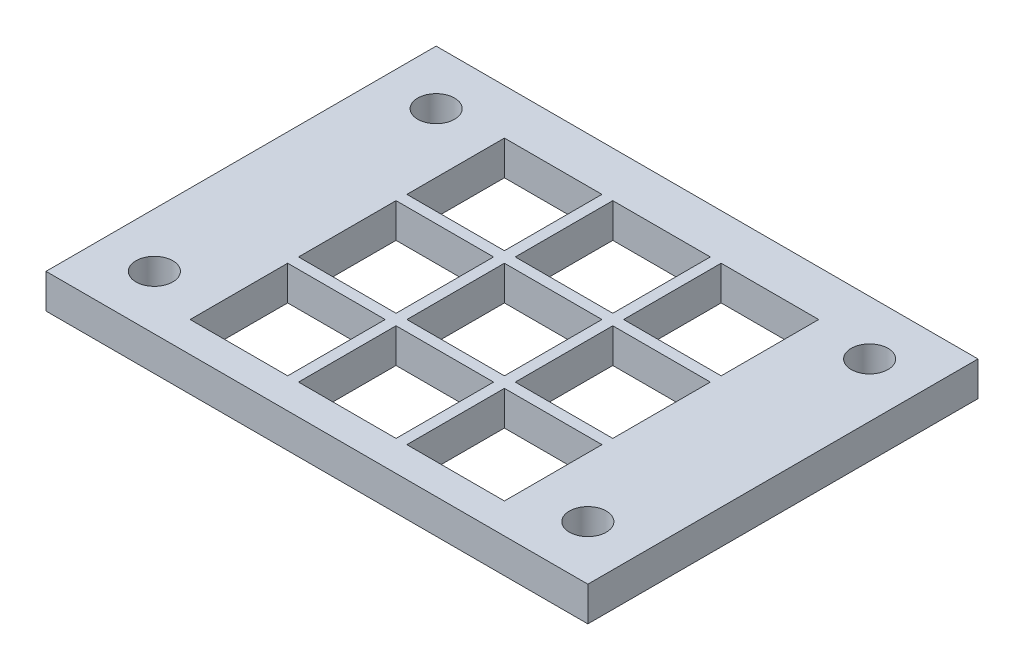
SolidWorks part; units mm, degrees
ref_plane "Front Plane" through (0, 0, 0) normal (0, 0, 1) x (1, 0, 0)
ref_plane "Top Plane" through (0, 0, 0) normal (0, 1, 0) x (1, 0, 0)
ref_plane "Right Plane" through (0, 0, 0) normal (1, 0, 0) x (0, 0, -1)
sketch "Sketch1" plane through (0, 0, 0) normal (0, 1, 0) x (1, 0, 0)
  line L0 (45, 31) -> (5, 31) construction
  line L1 (0, 0) -> (50, 0)
  line L2 (0, 0) -> (0, 36)
  line L3 (0, 36) -> (50, 36)
  line L4 (50, 0) -> (50, 36)
  line L6 (45, 31) -> (45, 5) construction
  line L8 (10.5, 11.8) -> (19.5, 11.8)
  line L9 (10.5, 11.8) -> (10.5, 2.8)
  line L10 (10.5, 2.8) -> (19.5, 2.8)
  line L11 (19.5, 11.8) -> (19.5, 2.8)
  line L12 (20.5, 11.8) -> (20.5, 2.8)
  line L13 (20.5, 11.8) -> (29.5, 11.8)
  line L14 (29.5, 11.8) -> (29.5, 2.8)
  line L15 (20.5, 2.8) -> (29.5, 2.8)
  line L16 (30.5, 11.8) -> (30.5, 2.8)
  line L17 (30.5, 11.8) -> (39.5, 11.8)
  line L18 (39.5, 11.8) -> (39.5, 2.8)
  line L19 (30.5, 2.8) -> (39.5, 2.8)
  line L20 (20.5, 21.8) -> (20.5, 12.8)
  line L21 (20.5, 21.8) -> (29.5, 21.8)
  line L22 (29.5, 21.8) -> (29.5, 12.8)
  line L23 (20.5, 12.8) -> (29.5, 12.8)
  line L24 (30.5, 21.8) -> (30.5, 12.8)
  line L25 (30.5, 21.8) -> (39.5, 21.8)
  line L26 (39.5, 21.8) -> (39.5, 12.8)
  line L27 (30.5, 12.8) -> (39.5, 12.8)
  line L28 (20.5, 31.8) -> (20.5, 22.8)
  line L29 (20.5, 31.8) -> (29.5, 31.8)
  line L30 (29.5, 31.8) -> (29.5, 22.8)
  line L31 (20.5, 22.8) -> (29.5, 22.8)
  line L32 (30.5, 31.8) -> (30.5, 22.8)
  line L33 (30.5, 31.8) -> (39.5, 31.8)
  line L34 (39.5, 31.8) -> (39.5, 22.8)
  line L35 (30.5, 22.8) -> (39.5, 22.8)
  line L36 (10.5, 21.8) -> (10.5, 12.8)
  line L37 (10.5, 21.8) -> (19.5, 21.8)
  line L38 (19.5, 21.8) -> (19.5, 12.8)
  line L39 (10.5, 12.8) -> (19.5, 12.8)
  line L40 (10.5, 31.8) -> (10.5, 22.8)
  line L41 (10.5, 31.8) -> (19.5, 31.8)
  line L42 (19.5, 31.8) -> (19.5, 22.8)
  line L43 (10.5, 22.8) -> (19.5, 22.8)
  circle A28 centre (5, 5) radius 1.7
  circle A29 centre (5, 31) radius 1.7
  circle A30 centre (45, 31) radius 1.7
  circle A31 centre (45, 5) radius 1.7
  point P7 (45, 18)
  point P9 (25, 31)
  point P10 (25, 36)
  point P12 (15, 2.8)
  point P20 (50, 18)
  dimension "D5" = 40
  dimension "D6" = 26
  dimension "D3" = 9
  dimension "D8" = 3.4
  dimension "D1" = 50
  dimension "D2" = 36
  dimension "D4" = 2.2
  dimension "D7" = 10
  dimension "D9" = 3
  dimension "D10" = 3
extrude "Boss-Extrude1" add sketch "Sketch1" along normal blind 3.175
equation "\"o\"= 10mm"
equation "\"P\"= 10"
